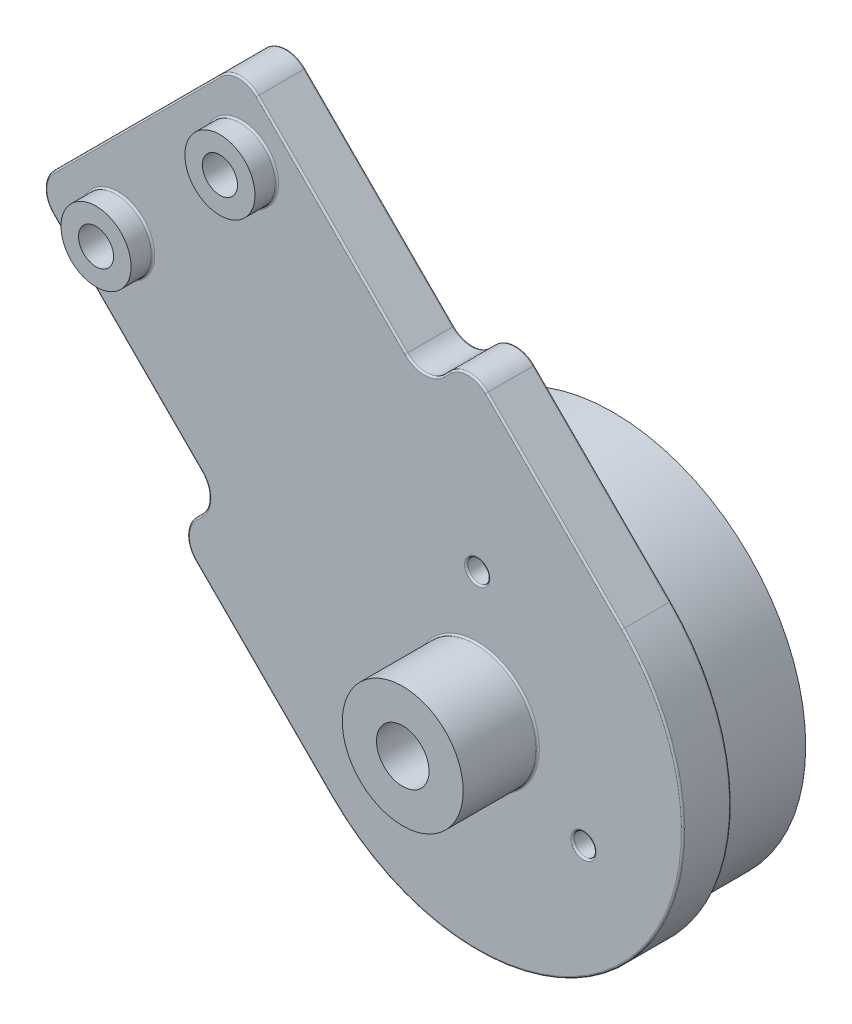
SolidWorks part; units mm, degrees
ref_plane "Front Plane" through (0, 0, 0) normal (0, 0, 1) x (1, 0, 0)
ref_plane "Top Plane" through (0, 0, 0) normal (0, 1, 0) x (1, 0, 0)
ref_plane "Right Plane" through (0, 0, 0) normal (1, 0, 0) x (0, 0, -1)
sketch "Sketch1" plane through (0, 0, 0) normal (0, 0, 1) x (1, 0, 0)
  line L0 (-100, 0) -> (100, 0) construction
  line L1 (-100, 0) -> (0, 100) construction
  line L2 (0, 100) -> (100, 0) construction
  line L3 (0, 100) -> (0, 60) construction
  line L4 (-40, 60) -> (40, 60) construction
  line L5 (0, 0) -> (-50, 50) construction
  circle A0 centre (-100, 0) radius 20
  circle A1 centre (0, 0) radius 20
  circle A2 centre (100, 0) radius 20
  point P4 (0, 0)
  point P9 (0, 60)
  dimension "D1" = 40
  dimension "D2" = 200
  dimension "D3" = 90
  dimension "D4" = 80
  dimension "D5" = 90
sketch "Sketch2" plane through (0, 0, 0) normal (0, 0, 1) x (1, 0, 0)
  line L0 (-56.5165, 43.4835) -> (-40, 60) construction
  line L1 (-100, 0) -> (0, 100) construction
  line L2 (-40, 60) -> (40, 60) construction
  line L3 (40, 60) -> (86.565, 13.435) construction
  line L4 (0, 100) -> (100, 0) construction
  line L5 (-49.4454, 36.4124) -> (-35.8579, 50)
  line L6 (-35.8579, 50) -> (35.8579, 50)
  line L7 (35.8579, 50) -> (79.4939, 6.364)
  line L8 (-63.5876, 50.5546) -> (-44.1421, 70)
  line L9 (-44.1421, 70) -> (44.1421, 70)
  line L10 (44.1421, 70) -> (93.636, 20.5061)
  line L11 (-63.5876, 50.5546) -> (-49.4454, 36.4124)
  line L12 (79.4939, 6.364) -> (93.636, 20.5061)
  line L13 (104.5962, 4.5962) -> (91.1612, 18.0312)
  line L14 (81.9688, 8.8388) -> (95.4038, -4.5962)
  line L15 (75.9584, 9.8995) -> (90.1005, 24.0416) construction
  line L16 (0, 100) -> (0, 60) construction
  line L17 (-3.4532, 85.4203) -> (-6, 70)
  line L18 (0, 84.85) -> (0, 84.8364) construction
  line L19 (3.4532, 85.4203) -> (6, 70)
  circle A0 centre (100, 0) radius 3.5
  circle A1 centre (100, 0) radius 10 construction
  arc A2 (95.4038, -4.5962) -> (104.5962, 4.5962) centre (100, 0) ccw
  circle A3 centre (79.4939, 13.435) radius 1
  circle A4 centre (100, 0) radius 6.5 construction
  circle A5 centre (86.565, 20.5061) radius 1
  circle A6 centre (0, 84.85) radius 1.5
  arc A7 (3.4532, 85.4203) -> (-3.4532, 85.4203) centre (0, 84.85) ccw
  circle A8 centre (0, 60) radius 1.5
  circle A9 centre (-50, 50) radius 1.5
  circle A10 centre (0, 84.85) radius 3.5 construction
  point P28 (106.5, 0)
  point P48 (3.5, 82)
  dimension "D4" = 7
  dimension "D5" = 20
  dimension "D9" = 2
  dimension "D11" = 14.85
  dimension "D12" = 3
  dimension "D14" = 6
  dimension "D15" = 3
  dimension "D1" = 10
  dimension "D3" = 27.5
  dimension "D7" = 19
  dimension "D8" = 5
  dimension "D10" = 5
  dimension "D2" = 10
  dimension "D6" = 3
  dimension "D13" = 2
sketch "Sketch3" plane through (0, 0, 0) normal (0, 0, 1) x (1, 0, 0)
  line L0 (-86.565, 13.435) -> (-50, 50) construction
  line L1 (-100, 0) -> (0, 100) construction
  line L2 (-50, 50) -> (-13.435, 13.435) construction
  line L3 (0, 0) -> (-50, 50) construction
  line L4 (-79.4939, 6.364) -> (-50, 35.8579)
  line L5 (-50, 35.8579) -> (-20.5061, 6.364)
  line L6 (-93.636, 20.5061) -> (-50, 64.1421)
  line L7 (-50, 64.1421) -> (-6.364, 20.5061)
  line L8 (-93.636, 20.5061) -> (-79.4939, 6.364)
  line L9 (-20.5061, 6.364) -> (-6.364, 20.5061)
  line L10 (-104.5962, 4.5962) -> (-91.1612, 18.0312)
  line L11 (-95.4038, -4.5962) -> (-81.9688, 8.8388)
  line L12 (-4.5962, -4.5962) -> (-18.0312, 8.8388)
  line L13 (4.534, 4.6576) -> (-9.0191, 17.8509)
  line L14 (-90.1005, 24.0416) -> (-75.9584, 9.8995) construction
  line L15 (-24.0416, 9.8995) -> (-9.8995, 24.0416) construction
  circle A0 centre (-100, 0) radius 3.5
  circle A1 centre (-100, 0) radius 10 construction
  circle A2 centre (0, 0) radius 3.5
  circle A3 centre (0, 0) radius 10 construction
  arc A4 (-4.5962, -4.5962) -> (4.534, 4.6576) centre (0, 0) ccw
  arc A5 (-104.5962, 4.5962) -> (-95.4038, -4.5962) centre (-100, 0) ccw
  circle A7 centre (0, 0) radius 20 construction
  circle A8 centre (-86.565, 20.5061) radius 1
  circle A9 centre (0, 0) radius 6.5 construction
  circle A10 centre (-79.4939, 13.435) radius 1
  circle A11 centre (-20.5061, 13.435) radius 1
  circle A12 centre (-13.435, 20.5061) radius 1
  circle A13 centre (-50, 50) radius 1.5 construction
  circle A14 centre (-50, 50) radius 1.5
  point P34 (6.5, 0)
  dimension "D1" = 7
  dimension "D2" = 20
  dimension "D4" = 10
  dimension "D10" = 2
  dimension "D6" = 19
  dimension "D7" = 19
  dimension "D8" = 5
  dimension "D9" = 5
  dimension "D11" = 5
  dimension "D12" = 5
  dimension "D3" = 3
  dimension "D5" = 10
sketch "Sketch4" plane through (0, 0, 0) normal (0, 0, 1) x (1, 0, 0)
  line L0 (0, 60) -> (0, 138.097) construction
  line L1 (-57.5, 93.3579) -> (57.5, 93.3579)
  line L2 (57.5, 93.3579) -> (57.5, 83.3579)
  line L3 (57.5, 83.3579) -> (44.1421, 70)
  line L4 (-44.1421, 70) -> (44.1421, 70) construction
  line L5 (44.1421, 70) -> (-44.1421, 70)
  line L6 (44.1421, 70) -> (93.636, 20.5061) construction
  line L7 (4, 60) -> (4, 70)
  line L8 (-4, 60) -> (-4, 70)
  line L9 (-57.5, 83.3579) -> (-44.1421, 70)
  line L10 (-57.5, 93.3579) -> (-57.5, 83.3579)
  line L11 (-22.5, 84.8579) -> (22.5, 84.8579) construction
  line L12 (-22.5, 89.3579) -> (22.5, 89.3579)
  line L13 (-22.5, 80.3579) -> (22.5, 80.3579)
  circle A0 centre (0, 60) radius 1.5 construction
  circle A1 centre (0, 60) radius 1.5
  arc A2 (-4, 60) -> (4, 60) centre (0, 60) ccw
  arc A3 (-22.5, 89.3579) -> (-22.5, 80.3579) centre (-22.5, 84.8579) ccw
  circle A4 centre (0, 60) radius 4 construction
  arc A5 (22.5, 80.3579) -> (22.5, 89.3579) centre (22.5, 84.8579) ccw
  point P23 (4, 60)
  point P25 (0, 70)
  point P27 (0, 93.3579)
  point P29 (0, 84.8579)
  dimension "D1" = 57.5
  dimension "D2" = 10
  dimension "D4" = 45
  dimension "D5" = 9
  dimension "D6" = 4
  dimension "D3" = 2.5
sketch "Sketch5" plane through (0, 0, 0) normal (0, 0, 1) x (1, 0, 0)
  line L0 (74.7209, 13.6118) -> (86.3882, 25.2791)
  line L2 (0, 100) -> (100, 0) construction
  line L3 (74.7209, 13.6118) -> (85.3275, 3.0052)
  line L4 (85.3275, 3.0052) -> (82.8527, 0.5303)
  line L5 (82.8527, 0.5303) -> (91.6915, -8.3085)
  line L6 (100, 0) -> (90.3746, 9.6254) construction
  line L7 (99.4697, 17.1473) -> (108.3085, 8.3085)
  line L8 (96.9948, 14.6725) -> (99.4697, 17.1473)
  line L9 (86.3882, 25.2791) -> (96.9948, 14.6725)
  circle A0 centre (100, 0) radius 10 construction
  circle A1 centre (100, 0) radius 10
  arc A2 (91.6915, -8.3085) -> (108.3085, 8.3085) centre (100, 0) ccw
  circle A3 centre (79.4939, 13.435) radius 1 construction
  circle A4 centre (100, 0) radius 11.75 construction
  circle A5 centre (86.565, 20.5061) radius 1 construction
  circle A6 centre (79.4939, 13.435) radius 1
  circle A7 centre (86.565, 20.5061) radius 1
  point P8 (80.5546, 19.4454)
  point P16 (111.75, 0)
  dimension "D2" = 16.5
  dimension "D3" = 15
  dimension "D4" = 12.5
  dimension "D1" = 1.75
extrude "Boss-Extrude1" add sketch "Sketch5" along normal blind 2.75
sketch "Sketch6" plane through (0, 0, 2.75) normal (0, 0, 1) x (1, 0, 0)
  circle A0 centre (100, 0) radius 10 construction
  circle A1 centre (100, 0) radius 10
extrude "Boss-Extrude2" add sketch "Sketch6" against normal blind 1
sketch "Sketch7" plane through (0, 0, 0) normal (0, 0, -1) x (-1, 0, 0)
  circle A0 centre (-100, 0) radius 10 construction
  circle A1 centre (-100, 0) radius 10
  circle A3 centre (-100, 0) radius 11
  dimension "D1" = 1
extrude "Boss-Extrude3" add sketch "Sketch7" along normal blind 5
fillet "Fillet1" radius 1.5 6 edges at (96.9948, 14.6725, 1.375) (99.4697, 17.1473, 1.375) (82.8527, 0.5303, 1.375) (85.3275, 3.0052, 1.375) (74.7209, 13.6118, 1.375) (86.3882, 25.2791, 1.375)
sketch "Sketch8" plane through (0, 0, 2.75) normal (0, 0, 1) x (1, 0, 0)
  circle A0 centre (79.4939, 13.435) radius 1 construction
  circle A1 centre (86.565, 20.5061) radius 1 construction
  circle A2 centre (79.4939, 13.435) radius 1
  circle A3 centre (86.565, 20.5061) radius 1
  circle A4 centre (86.565, 20.5061) radius 2
  circle A5 centre (79.4939, 13.435) radius 2
  dimension "D1" = 1
extrude "Boss-Extrude4" add sketch "Sketch8" along normal blind 1.25
sketch "Sketch9" plane through (0, 0, 2.75) normal (0, 0, 1) x (1, 0, 0)
  circle A0 centre (100, 0) radius 1.5
  dimension "D1" = 3
extrude "Cut-Extrude1" cut sketch "Sketch9" against normal through all
sketch "Sketch10" plane through (0, 0, 2.75) normal (0, 0, 1) x (1, 0, 0)
  circle A0 centre (100, 0) radius 3.45
  circle A1 centre (100, 0) radius 1.5 construction
  circle A2 centre (100, 0) radius 1.5
  dimension "D1" = 6.9
extrude "Boss-Extrude5" add sketch "Sketch10" along normal blind 4.25
sketch "Sketch11" plane through (0, 0, 2.75) normal (0, 0, 1) x (1, 0, 0)
  circle A0 centre (100, 0) radius 7 construction
  circle A1 centre (100, 7) radius 0.625
  circle A2 centre (106.0622, -3.5) radius 0.625
  circle A3 centre (93.9378, -3.5) radius 0.625
  point P12 (100, 0)
  dimension "D1" = 14
  dimension "D2" = 1.25
  dimension "D3" = 3
extrude "Cut-Extrude2" cut sketch "Sketch11" against normal through all
fillet "Fillet2" radius 0.1 42 edges at (110, 0, 1.75) (101.5, 0, 1.75) (94.5628, -3.5, 1.75) (106.6872, -3.5, 1.75) (100.625, 7, 1.75) (111, 0, 0) (96.9948, 15.2938, 0) (91.6915, 19.9758, 0) (86.3882, 24.6577, 0) (80.5546, 19.4454, 0) (75.3423, 13.6118, 0) (80.0242, 8.3085, 0) (84.7062, 3.0052, 0) (84.0901, 1.7678, 0) (83.474, 0.5303, 0) (87.8024, -4.4194, 0) (108.3085, -8.3085, 0) (104.4194, 12.1976, 0) (99.4697, 16.526, 0) (98.2322, 15.9099, 0) (80.4939, 13.435, 0) (87.565, 20.5061, 0) (103.45, 0, 2.75) (88.565, 20.5061, 2.75) (108.3085, -8.3085, 2.75) (87.8024, -4.4194, 2.75) (83.474, 0.5303, 2.75) (84.0901, 1.7678, 2.75) (84.7062, 3.0052, 2.75) (80.0242, 8.3085, 2.75) (75.3423, 13.6118, 2.75) (80.5546, 19.4454, 2.75) (86.3882, 24.6577, 2.75) (91.6915, 19.9758, 2.75) (96.9948, 15.2938, 2.75) (98.2322, 15.9099, 2.75) (99.4697, 16.526, 2.75) (104.4194, 12.1976, 2.75) (81.4939, 13.435, 2.75) (94.5628, -3.5, 2.75) (106.6872, -3.5, 2.75) (100.625, 7, 2.75)
